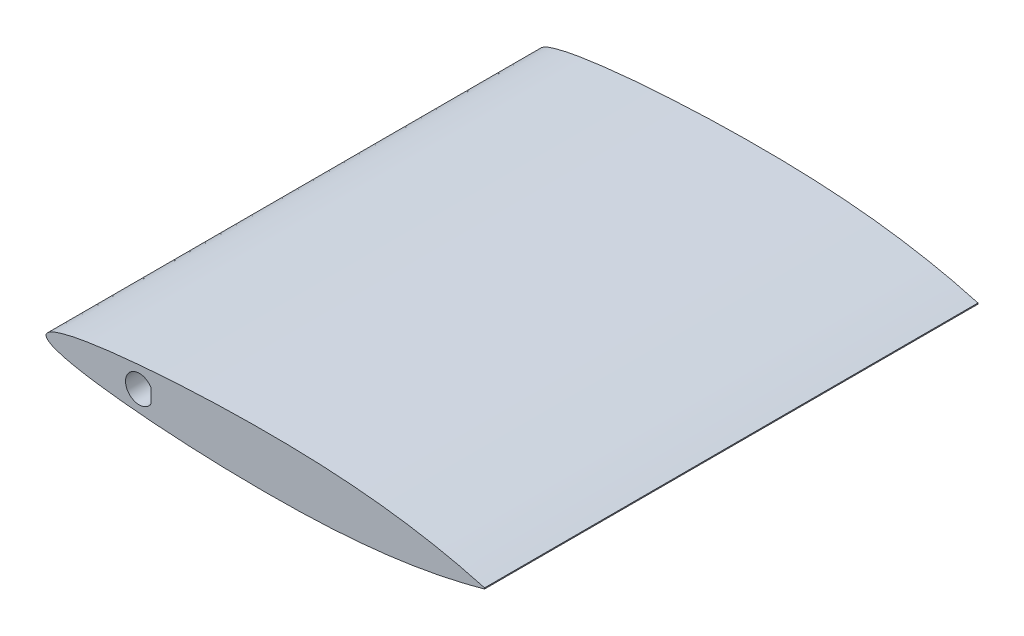
SolidWorks part; units mm, degrees
material "Maple"
ref_plane "Front Plane" through (0, 0, 0) normal (0, 0, 1) x (1, 0, 0)
ref_plane "Top Plane" through (0, 0, 0) normal (0, 1, 0) x (1, 0, 0)
ref_plane "Right Plane" through (0, 0, 0) normal (1, 0, 0) x (0, 0, -1)
curve "Curve3"
  spline degree 3 poles (101.6, 0.1219, 0) (99.9099, 0.5738, 0) (96.5445, 1.4735, 0) (89.7838, 2.9471, 0) (81.3219, 4.3668, 0) (71.1403, 5.4364, 0) (60.9671, 5.9966, 0) (50.8, 6.1452, 0) (40.6357, 5.9983, 0) (30.4708, 5.553, 0) (22.003, 4.9329, 0) (15.2308, 4.2232, 0) (10.9987, 3.6642, 0) (7.608, 3.0922, 0) (5.0721, 2.5808, 0) (2.8944, 1.9709, 0) (1.1817, 1.3642, 0) (-0.6746, 0, 0) (1.1817, -1.3642, 0) (2.8944, -1.9709, 0) (5.0721, -2.5808, 0) (7.608, -3.0922, 0) (10.9987, -3.6642, 0) (15.2308, -4.2232, 0) (22.003, -4.9329, 0) (30.4708, -5.553, 0) (40.6357, -5.9983, 0) (50.8, -6.1452, 0) (60.9671, -5.9966, 0) (71.1403, -5.4364, 0) (81.3219, -4.3668, 0) (89.7838, -2.9471, 0) (96.5445, -1.4735, 0) (99.9099, -0.5738, 0) (101.6, -0.1219, 0) knots 0 0 0 0 0.025456 0.050691 0.100669 0.150236 0.199601 0.248894 0.298185 0.347518 0.396944 0.421725 0.446593 0.459091 0.47168 0.48448 0.49114 0.5 0.50886 0.51552 0.52832 0.540909 0.553407 0.578275 0.603056 0.652482 0.701815 0.751106 0.800399 0.849764 0.899331 0.949309 0.974544 1 1 1 1
sketch "Sketch1" plane through (0, 0, 0) normal (0, 0, 1) x (1, 0, 0)
  line L0 (101.6, 0.1219) -> (101.6, -0.1219)
  spline S0 degree 3 poles (2808.3329, 9617.4645) (272.8572, -211.1663) (203.3622, -21.8091) (89.7838, 2.9471) (81.3219, 4.3668) (71.1403, 5.4364) (60.9671, 5.9966) (50.8, 6.1452) (40.6357, 5.9983) (30.4708, 5.553) (22.003, 4.9329) (15.2308, 4.2232) (10.9987, 3.6642) (7.608, 3.0922) (5.0721, 2.5808) (2.8944, 1.9709) (1.1817, 1.3642) (-0.6746, 0) (1.1817, -1.3642) (2.8944, -1.9709) (5.0721, -2.5808) (7.608, -3.0922) (10.9987, -3.6642) (15.2308, -4.2232) (22.003, -4.9329) (30.4708, -5.553) (40.6357, -5.9983) (50.8, -6.1452) (60.9671, -5.9966) (71.1403, -5.4364) (81.3219, -4.3668) (89.7838, -2.9471) (203.3598, 21.8086) (272.8542, 211.1583) (2808.1686, -9616.8277) knots -1.590548 -1.590548 -1.590548 -1.590548 0.025456 0.050691 0.100669 0.150236 0.199601 0.248894 0.298185 0.347518 0.396944 0.421725 0.446593 0.459091 0.47168 0.48448 0.49114 0.5 0.50886 0.51552 0.52832 0.540909 0.553407 0.578275 0.603056 0.652482 0.701815 0.751106 0.800399 0.849764 0.899331 0.949309 0.974544 2.590514 2.590514 2.590514 2.590514 only from (101.6, 0.1219) to (101.6, -0.1219) construction
  spline S1 degree 3 poles (101.6, 0.1219) (99.9099, 0.5738) (96.5445, 1.4735) (89.7838, 2.9471) (81.3219, 4.3668) (71.1403, 5.4364) (60.9671, 5.9966) (50.8, 6.1452) (40.6357, 5.9983) (30.4708, 5.553) (22.003, 4.9329) (15.2308, 4.2232) (10.9987, 3.6642) (7.608, 3.0922) (5.0721, 2.5808) (2.8944, 1.9709) (1.1817, 1.3642) (-0.6746, 0) (1.1817, -1.3642) (2.8944, -1.9709) (5.0721, -2.5808) (7.608, -3.0922) (10.9987, -3.6642) (15.2308, -4.2232) (22.003, -4.9329) (30.4708, -5.553) (40.6357, -5.9983) (50.8, -6.1452) (60.9671, -5.9966) (71.1403, -5.4364) (81.3219, -4.3668) (89.7838, -2.9471) (96.5445, -1.4735) (99.9099, -0.5738) (101.6, -0.1219) knots 0 0 0 0 0.025456 0.050691 0.100669 0.150236 0.199601 0.248894 0.298185 0.347518 0.396944 0.421725 0.446593 0.459091 0.47168 0.48448 0.49114 0.5 0.50886 0.51552 0.52832 0.540909 0.553407 0.578275 0.603056 0.652482 0.701815 0.751106 0.800399 0.849764 0.899331 0.949309 0.974544 1 1 1 1
extrude "Boss-Extrude1" add sketch "Sketch1" along normal blind 114.3
sketch "Sketch2" plane through (0, 0, 114.3) normal (0, 0, 1) x (1, 0, 0)
  line L1 (101.6, 0.1219) -> (101.6, -0.1219)
  line L4 (24.3496, 1.5875) -> (24.3496, -1.5875)
  arc A0 (24.3496, 1.5875) -> (24.3496, -1.5875) centre (21.6, 0) ccw
  dimension "D1" = 6.35
  dimension "D2" = 3.175
  dimension "D3" = 80
extrude "Cut-Extrude1" cut sketch "Sketch2" against normal through all contours L4 A0
